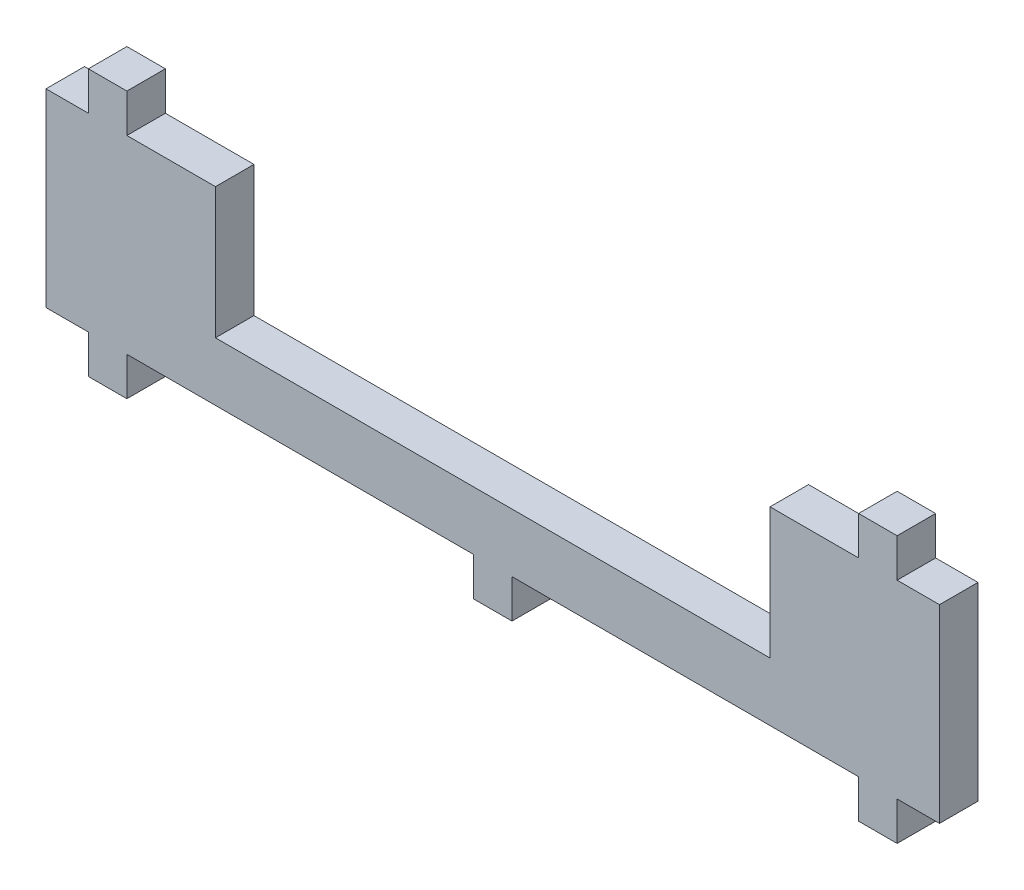
SolidWorks part; units mm, degrees
ref_plane "Front" through (0, 0, 0) normal (0, 0, 1) x (1, 0, 0)
ref_plane "Top" through (0, 0, 0) normal (0, 1, 0) x (1, 0, 0)
ref_plane "Right" through (0, 0, 0) normal (1, 0, 0) x (0, 0, -1)
sketch "Sketch1" plane through (0, 0, 0) normal (0, 0, 1) x (1, 0, 0)
  line L1 (-58, -6.15) -> (58, -6.15)
  line L2 (-58, -6.15) -> (-58, 6.15)
  line L3 (-58, 6.15) -> (58, 6.15)
  line L4 (58, -6.15) -> (58, 6.15)
  line L5 (-58, -6.15) -> (58, 6.15) construction
  line L6 (-58, 6.15) -> (58, -6.15) construction
  point P0 (0, 0)
  dimension "D1" = 12.3
  dimension "D2" = 116
extrude "Boss-Extrude1" add sketch "Sketch1" along normal blind 5
sketch "Sketch2" plane through (0, -6.15, 0) normal (0, -1, 0) x (1, 0, 0)
  line L0 (-58, 5) -> (58, 5) construction
  line L1 (-52.5, 5) -> (-47.5, 5)
  line L2 (-52.5, 5) -> (-52.5, 0)
  line L3 (-52.5, 0) -> (-47.5, 0)
  line L4 (-47.5, 5) -> (-47.5, 0)
  line L5 (-58, 0) -> (58, 0) construction
  line L6 (-58, 5) -> (-58, 0) construction
  line L11 (47.5, 5) -> (52.5, 5)
  line L12 (47.5, 5) -> (47.5, 0)
  line L13 (47.5, 0) -> (52.5, 0)
  line L14 (52.5, 5) -> (52.5, 0)
  point P16 (-58, 2.5)
  dimension "D1" = 5
  dimension "D3" = 5
  dimension "D5" = 95
  dimension "D6" = 5.5
extrude "Boss-Extrude2" add sketch "Sketch2" along normal blind 5
mirror "Mirror1" about plane through (-58, 6.15, 5) normal (0, -1, 0) of bodies 102
sketch "Sketch3" plane through (0, 18.45, 0) normal (0, 1, 0) x (1, 0, 0)
  line L0 (-47.5, 0) -> (47.5, 0) construction
  line L1 (-36, 0) -> (36, 0)
  line L2 (-36, 0) -> (-36, -5)
  line L3 (-36, -5) -> (36, -5)
  line L4 (36, 0) -> (36, -5)
  line L5 (-47.5, -5) -> (47.5, -5) construction
  line L6 (-58, -5) -> (-58, 0) construction
  dimension "D1" = 72
  dimension "D2" = 22
extrude "Cut-Extrude1" cut sketch "Sketch3" against normal blind 17
sketch "Sketch4" plane through (0, -6.15, 0) normal (0, -1, 0) x (1, 0, 0)
  line L0 (-47.5, 5) -> (47.5, 5) construction
  line L1 (-2.5, 5) -> (2.5, 5)
  line L2 (-2.5, 5) -> (-2.5, 0)
  line L3 (-2.5, 0) -> (2.5, 0)
  line L4 (2.5, 5) -> (2.5, 0)
  line L5 (-47.5, 0) -> (47.5, 0) construction
  line L6 (-47.5, 0) -> (-47.5, 5) construction
  dimension "D1" = 5
  dimension "D2" = 45
extrude "Boss-Extrude3" add sketch "Sketch4" along normal blind 5
